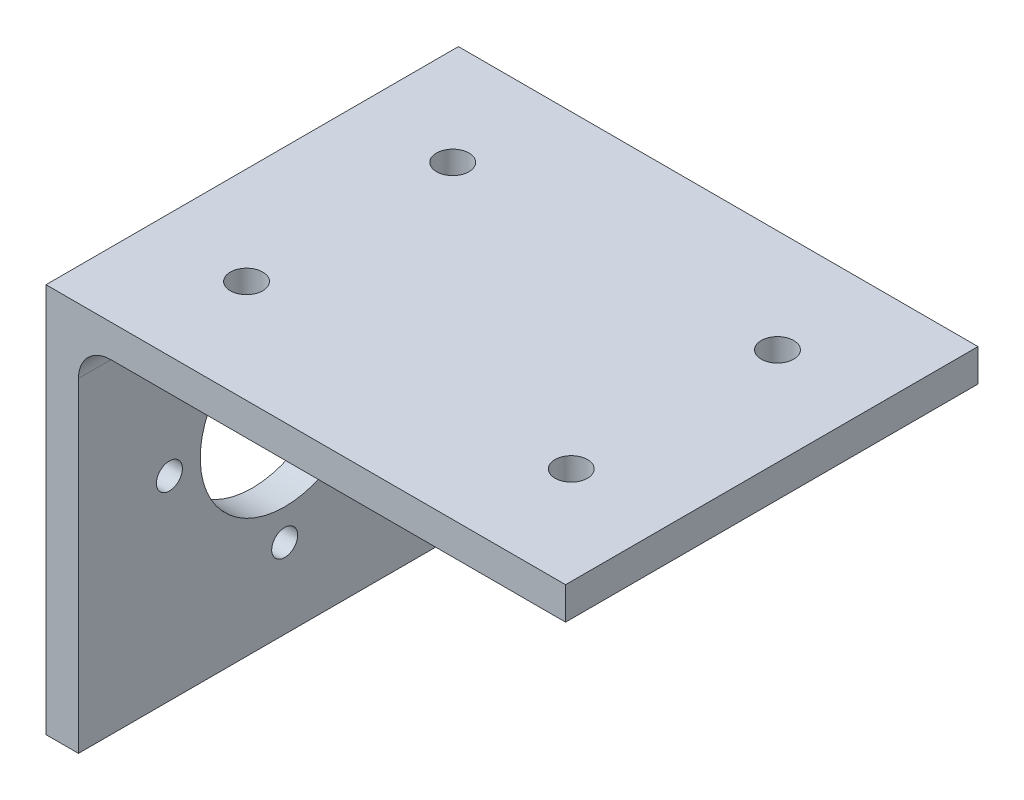
SolidWorks part; units mm, degrees
ref_plane "Front Plane" through (0, 0, 0) normal (0, 0, 1) x (1, 0, 0)
ref_plane "Top Plane" through (0, 0, 0) normal (0, 1, 0) x (1, 0, 0)
ref_plane "Right Plane" through (0, 0, 0) normal (1, 0, 0) x (0, 0, -1)
sketch "Sketch1" plane through (0, 0, 0) normal (0, 0, 1) x (1, 0, 0)
  line L0 (-108.5502, 0) -> (108.5502, 0) construction
  line L1 (0, 113.7546) -> (0, -113.7546) construction
  line L2 (0, 0) -> (0, 60)
  line L3 (0, 60) -> (80, 60)
  line L4 (80, 60) -> (80, 55)
  line L5 (80, 55) -> (10, 55)
  line L6 (5, 50) -> (5, 0)
  line L7 (5, 0) -> (0, 0)
  arc A0 (10, 55) -> (5, 50) centre (10, 50) ccw
  point P5 (0, 0)
  point P6 (0, 0)
  dimension "D5" = 5
  dimension "D1" = 80
  dimension "D2" = 60
  dimension "D3" = 5
  dimension "D4" = 5
extrude "Boss-Extrude1" add sketch "Sketch1" along normal blind 63.5
sketch "Sketch2" plane through (0, 0, 0) normal (-1, 0, 0) x (0, 0, 1)
  line L0 (0, 30) -> (63.5, 30) construction
  line L1 (0, 60) -> (0, 0) construction
  line L2 (63.5, 60) -> (63.5, 0) construction
  line L4 (63.5, 60) -> (0, 60) construction
  line L5 (31.75, 60) -> (31.75, 0) construction
  line L6 (63.5, 0) -> (0, 0) construction
  circle A0 centre (31.75, 30) radius 13
  circle A2 centre (49.5, 30) radius 2
  circle A3 centre (31.75, 12.25) radius 2
  circle A4 centre (14, 30) radius 2
  circle A5 centre (31.75, 47.75) radius 2
  dimension "D1" = 26
  dimension "D2" = 4
  dimension "D3" = 17.75
  dimension "D4" = 4
extrude "Cut-Extrude1" cut sketch "Sketch2" against normal blind 5
sketch "Sketch3" plane through (0, 60, 0) normal (0, 1, 0) x (1, 0, 0)
  line L0 (40, 0) -> (40, -63.5) construction
  line L1 (80, 0) -> (0, 0) construction
  line L2 (80, -63.5) -> (0, -63.5) construction
  line L3 (0, -31.75) -> (80, -31.75) construction
  line L4 (0, -63.5) -> (0, 0) construction
  line L5 (80, -63.5) -> (80, 0) construction
  circle A4 centre (15, -15.875) radius 2.5
  circle A5 centre (65, -15.875) radius 2.5
  circle A6 centre (65, -47.625) radius 2.5
  circle A7 centre (15, -47.625) radius 2.5
  point P14 (40, -31.75)
  dimension "D2" = 50
  dimension "D1" = 5
  dimension "D3" = 15.875
extrude "Cut-Extrude2" cut sketch "Sketch3" against normal blind 5
